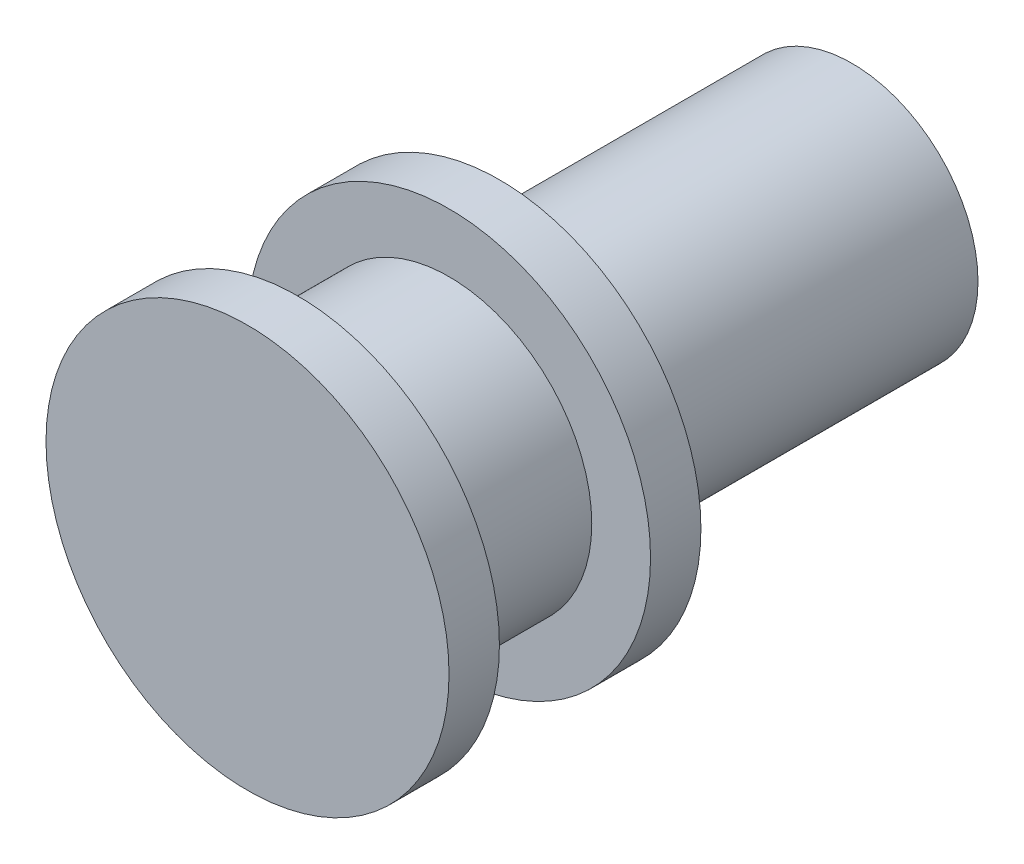
SolidWorks part; units mm, degrees
material "Brass"
ref_plane "Front Plane" through (0, 0, 0) normal (0, 0, 1) x (1, 0, 0)
ref_plane "Top Plane" through (0, 0, 0) normal (0, 1, 0) x (1, 0, 0)
ref_plane "Right Plane" through (0, 0, 0) normal (1, 0, 0) x (0, 0, -1)
sketch "Sketch2" plane through (0, 0, 0) normal (1, 0, 0) x (0, 0, -1)
  line L0 (-2.4509, 0) -> (7.016, 0) construction
  line L1 (0, 0) -> (0, 3.048)
  line L2 (0, 3.048) -> (0.762, 3.048)
  line L3 (0.762, 3.048) -> (0.762, 2.159)
  line L4 (0.762, 2.159) -> (3.048, 2.159)
  line L5 (3.048, 2.159) -> (3.048, 3.048)
  line L6 (3.048, 3.048) -> (3.81, 3.048)
  line L7 (3.81, 3.048) -> (3.81, 1.905)
  line L8 (3.81, 1.905) -> (9.144, 1.905)
  line L9 (9.144, 1.905) -> (9.144, 0)
  line L10 (0, 0) -> (9.144, 0)
  dimension "D1" = 1.905
  dimension "D2" = 3.048
  dimension "D3" = 2.159
  dimension "D4" = 3.048
  dimension "D5" = 9.144
  dimension "D6" = 0.762
  dimension "D7" = 2.286
  dimension "D8" = 0.762
revolve "Revolve1" add sketch "Sketch2" angle 360 about L0
